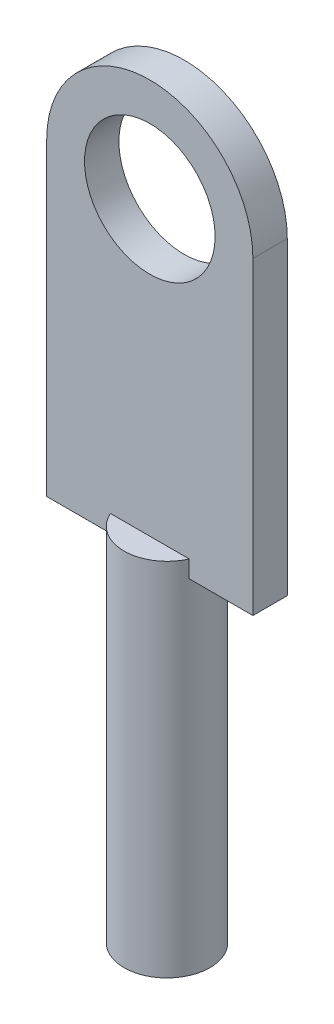
SolidWorks part; units mm, degrees
material "Brass"
ref_plane "Front Plane" through (0, 0, 0) normal (0, 0, 1) x (1, 0, 0)
ref_plane "Top Plane" through (0, 0, 0) normal (0, 1, 0) x (1, 0, 0)
ref_plane "Right Plane" through (0, 0, 0) normal (1, 0, 0) x (0, 0, -1)
sketch "Sketch1" plane through (0, 0, 0) normal (0, 1, 0) x (1, 0, 0)
  circle A0 centre (0, 0) radius 1.5875
  dimension "D1" = 3.175
extrude "Extrude1" add sketch "Sketch1" along normal blind 8.255
sketch "Sketch2" plane through (0, 0, 0) normal (0, 0, 1) x (1, 0, 0)
  line L0 (-3.81, 19.05) -> (-3.81, 7.62)
  line L1 (-3.81, 7.62) -> (3.81, 7.62)
  line L2 (3.81, 19.05) -> (3.81, 7.62)
  line L4 (1.5875, 8.255) -> (-1.5875, 8.255) construction
  arc A0 (3.81, 19.05) -> (-3.81, 19.05) centre (0, 19.05) ccw
  circle A1 centre (0, 19.05) radius 2.413
  dimension "D1" = 4.826
  dimension "D2" = 7.62
  dimension "D3" = 19.05
  dimension "D4" = 0.635
extrude "Extrude2" add sketch "Sketch2" along normal mid plane 1.27
sketch "Sketch3" plane through (0, 0, 0) normal (0, -1, 0) x (1, 0, 0)
  circle A0 centre (0, 0) radius 1.5875
extrude "Extrude3" add sketch "Sketch3" along normal blind 5.08
